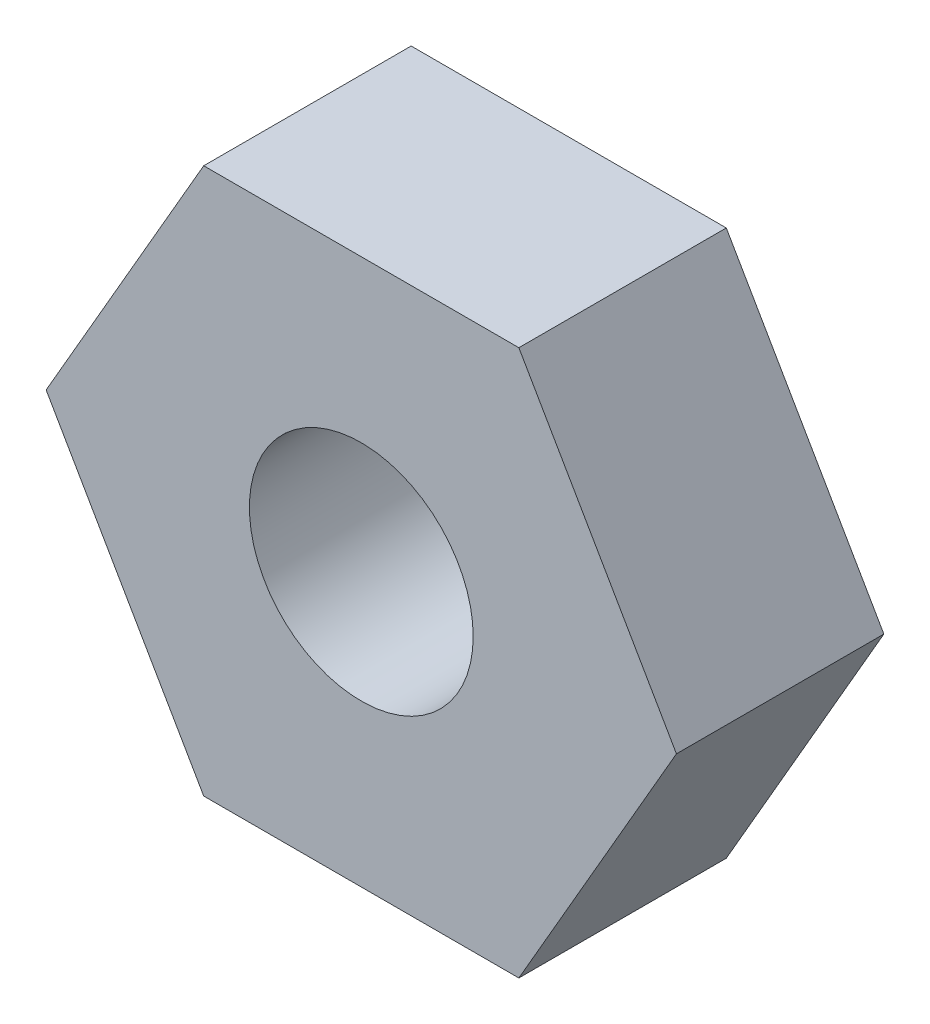
SolidWorks part; units mm, degrees
material "1060 合金"
ref_plane "前视基准面" through (0, 0, 0) normal (0, 0, 1) x (1, 0, 0)
ref_plane "上视基准面" through (0, 0, 0) normal (0, 1, 0) x (1, 0, 0)
ref_plane "右视基准面" through (0, 0, 0) normal (1, 0, 0) x (0, 0, -1)
sketch "草图1" plane through (0, 0, 0) normal (0, 0, 1) x (1, 0, 0)
  line L1 (-2.8868, 0) -> (-1.4434, -2.5)
  line L2 (-1.4434, -2.5) -> (1.4434, -2.5)
  line L3 (1.4434, -2.5) -> (2.8868, 0)
  line L4 (2.8868, 0) -> (1.4434, 2.5)
  line L5 (1.4434, 2.5) -> (-1.4434, 2.5)
  line L6 (-1.4434, 2.5) -> (-2.8868, 0)
  circle A0 centre (0, 0) radius 2.5 construction
  dimension "D1" = 5
extrude "凸台-拉伸1" add sketch "草图1" along normal blind 1.9
hole_wizard "M2.5 螺纹孔1" positions "草图2" profile "草图3" tap size "M2.5" standard "GB" end condition through all
sketch "草图2" plane through (0, 0, 1.9) normal (0, 0, 1) x (1, 0, 0)
  point P0 (0, 0)
sketch "草图3" plane through (0, 0, 1.9) normal (1, 0, 0) x (0, -1, 0)
  line L0 (0, 0) -> (0, 1.9)
  line L1 (0, 1.9) -> (1.025, 1.9)
  line L2 (1.025, 1.9) -> (1.025, 0)
  line L5 (1.025, 0) -> (0, 0)
  line L11 (0, -6.35) -> (0, 107.95) construction
  dimension "通孔螺纹孔钻头直径" = 2.05
  dimension "通孔螺纹孔钻头深度" = 1.9
cosmetic thread "孔螺蚊线1" parameters "D2"=2.5
